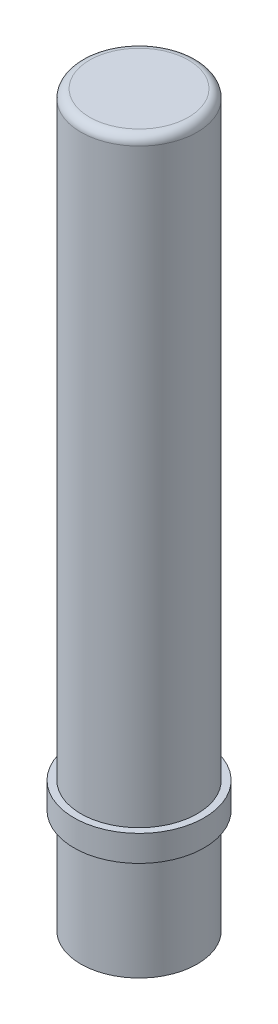
SolidWorks part; units mm, degrees
ref_plane "Front Plane" through (0, 0, 0) normal (0, 0, 1) x (1, 0, 0)
ref_plane "Top Plane" through (0, 0, 0) normal (0, 1, 0) x (1, 0, 0)
ref_plane "Right Plane" through (0, 0, 0) normal (1, 0, 0) x (0, 0, -1)
sketch "Sketch1" plane through (0, 0, 0) normal (0, 1, 0) x (1, 0, 0)
  circle A0 centre (0, 0) radius 3.35
  dimension "D1" = 6.7
extrude "Boss-Extrude1" add sketch "Sketch1" along normal blind 42
ref_plane "Plane1" through (0, 6, 0) normal (0, -1, 0) x (-1, 0, 0)
sketch "Sketch4" plane through (0, 6, 0) normal (0, -1, 0) x (-1, 0, 0)
  circle A0 centre (0, 0) radius 3.75
  dimension "D1" = 7.5
extrude "Boss-Extrude3" add sketch "Sketch4" against normal blind 1.5
fillet "Fillet1" radius 0.5 1 edges at (0, 42, 3.35)
